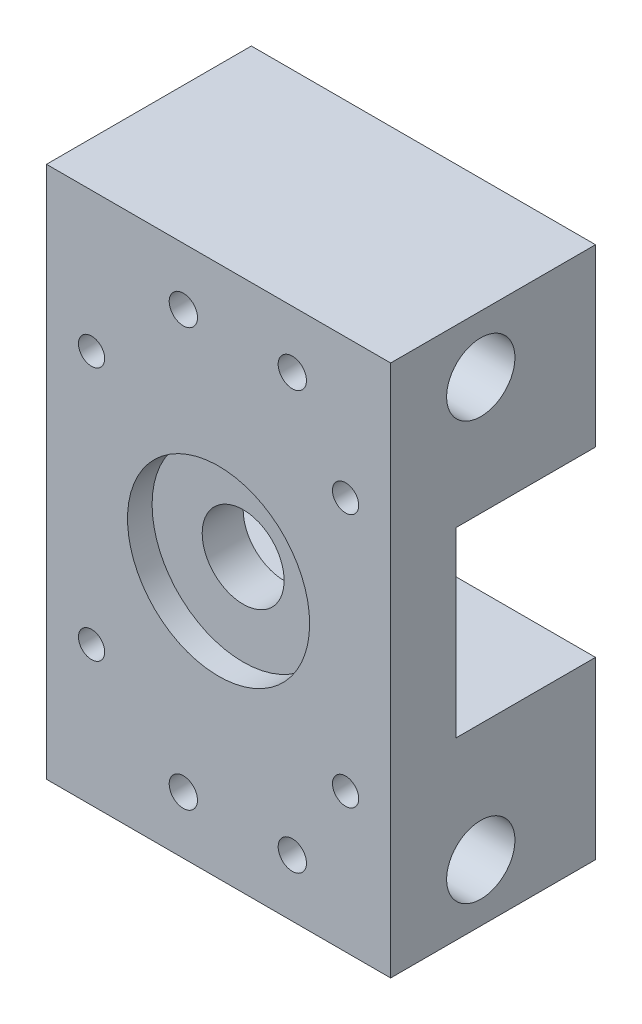
SolidWorks part; units mm, degrees
ref_plane "Plano frontal" through (0, 0, 0) normal (0, 0, 1) x (1, 0, 0)
ref_plane "Plano superior" through (0, 0, 0) normal (0, 1, 0) x (1, 0, 0)
ref_plane "Plano direito" through (0, 0, 0) normal (1, 0, 0) x (0, 0, -1)
ref_plane "Plano1" through (0, 0, 21) normal (0, 0, 1) x (1, 0, 0)
sketch "Esboço1" plane through (0, 0, 21) normal (0, 0, 1) x (1, 0, 0)
  line L0 (0, 65) -> (0, 0)
  line L1 (0, 0) -> (42, 0)
  line L2 (42, 0) -> (42, 65)
  line L3 (42, 65) -> (0, 65)
extrude "Ressalto-extrusão1" add sketch "Esboço1" against normal blind 21
sketch "Esboço2" plane through (42, 0, 0) normal (1, 0, 0) x (0, 0, -1)
  line L0 (0, 21.3875) -> (0, 43.6125)
  line L1 (0, 43.6125) -> (-17, 43.6125)
  line L2 (-17, 43.6125) -> (-17, 21.3875)
  line L3 (-17, 21.3875) -> (0, 21.3875)
extrude "Corte-extrusão1" cut sketch "Esboço2" against normal through all
hole_wizard "Furo com folga de M31" positions "Esboço4" profile "Esboço3" hole size "M3" standard "Ansi Metric"
sketch "Esboço4" plane through (0, 0, 0) normal (0, 0, -1) x (-1, 0, 0)
  point P0 (-30, 7)
  point P1 (-16.7, 7)
  point P2 (-16.7, 58)
  point P3 (-30, 58)
sketch "Esboço3" plane through (30, 7, 0) normal (1, 0, 0) x (0, 1, 0)
  line L0 (0, 0) -> (0, 21)
  line L1 (0, 21) -> (1.7272, 21)
  line L2 (1.7272, 21) -> (1.7272, 0)
  line L5 (1.7272, 0) -> (0, 0)
  line L11 (0, -6.35) -> (0, 107.95) construction
  dimension "Thru Hole Dia." = 3.4544
  dimension "Thru Hole Depth" = 21
hole_wizard "Furo com folga de M201" positions "Esboço6" profile "Esboço5" hole size "M20" standard "Ansi Metric"
sketch "Esboço6" plane through (0, 0, 21) normal (0, 0, 1) x (1, 0, 0)
  point P0 (21, 32.5)
sketch "Esboço5" plane through (21, 32.5, 21) normal (1, 0, 0) x (0, -1, 0)
  line L0 (0, 0) -> (0, 21)
  line L1 (0, 21) -> (11.1125, 21)
  line L2 (11.1125, 21) -> (11.1125, 0)
  line L5 (11.1125, 0) -> (0, 0)
  line L11 (0, -6.35) -> (0, 107.95) construction
  dimension "Thru Hole Dia." = 22.225
  dimension "Thru Hole Depth" = 21
hole_wizard "Rebaixo para parafuso de máquina de cabeça sextavada de M31" positions "Esboço8" profile "Esboço7" counterbore size "M3" standard "Ansi Metric"
sketch "Esboço8" plane through (0, 0, 0) normal (0, 0, -1) x (-1, 0, 0)
  point P0 (-36.5, 17)
  point P1 (-5.5, 17)
  point P2 (-5.5, 48)
  point P3 (-36.5, 48)
sketch "Esboço7" plane through (36.5, 17, 0) normal (1, 0, 0) x (0, 1, 0)
  line L0 (0, 0) -> (0, 21)
  line L1 (0, 21) -> (1.6, 21)
  line L3 (1.6, 21) -> (1.6, 7.62)
  line L4 (1.6, 7.62) -> (3, 7.62)
  line L5 (3, 7.62) -> (3, 0)
  line L7 (3, 0) -> (0, 0)
  line L11 (0, -6.35) -> (0, 107.95) construction
  dimension "Thru Hole Dia." = 3.2
  dimension "Thru Hole Depth" = 21
  dimension "C'Bore Dia." = 6
  dimension "C'Bore Depth" = 7.62
hole_wizard "Furo1" positions "Esboço10" profile "Esboço9" legacy
sketch "Esboço10" plane through (42, 0, 0) normal (1, 0, 0) x (0, 0, -1)
  point P0 (-14, 7)
  point P1 (-14, 58)
sketch "Esboço9" plane through (42, 7, 14) normal (0, 1, 0) x (0, 0, -1)
  line L0 (0, 0) -> (0, 8)
  line L1 (0, 8) -> (4.1672, 8)
  line L2 (4.1672, 8) -> (4.1672, 0)
  line L3 (4.1672, 0) -> (0, 0)
  line L4 (0, 110) -> (0, -10) construction
  dimension "Diameter" = 8.3344
  dimension "Depth" = 8
sketch "Esboço11" plane through (0, 0, 21) normal (0, 0, 1) x (1, 0, 0)
  line L1 (0, 65) -> (42, 65)
  line L2 (0, 65) -> (0, 0)
  line L3 (0, 0) -> (42, 0)
  line L4 (42, 65) -> (42, 0)
  circle A0 centre (21, 32.5) radius 11.1125
  circle A1 centre (16.7, 7) radius 1.7272
  circle A2 centre (30, 7) radius 1.7272
  circle A3 centre (5.5, 17) radius 1.6
  circle A4 centre (5.5, 48) radius 1.6
  circle A5 centre (16.7, 58) radius 1.7272
  circle A6 centre (36.5, 48) radius 1.6
  circle A7 centre (30, 58) radius 1.7272
  circle A8 centre (36.5, 17) radius 1.6
extrude "Ressalto-extrusão2" add sketch "Esboço11" along normal blind 4
sketch "Esboço13" plane through (0, 0, 17) normal (0, 0, -1) x (-1, 0, 0)
  circle A0 centre (-21, 32.5) radius 5
  circle A1 centre (-21, 32.5) radius 11.1125
extrude "Ressalto-extrusão3" add sketch "Esboço13" against normal blind 5
